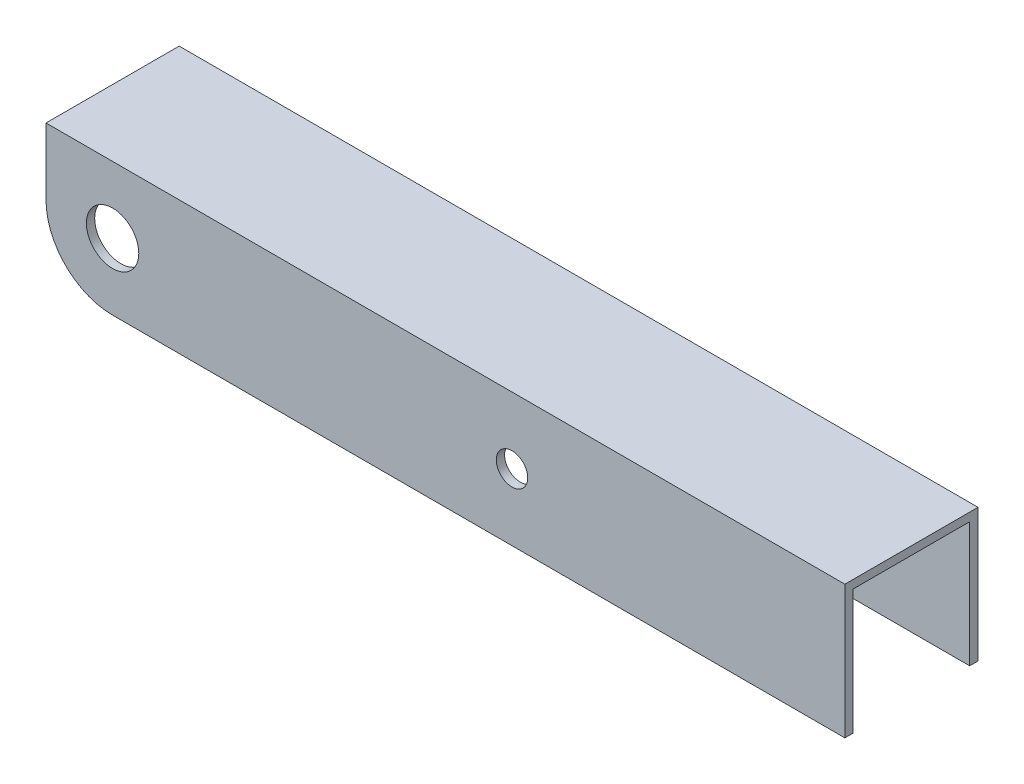
SolidWorks part; units mm, degrees
material "6061-T6 (SS)"
ref_plane "Front Plane" through (0, 0, 0) normal (0, 0, 1) x (1, 0, 0)
ref_plane "Top Plane" through (0, 0, 0) normal (0, 1, 0) x (1, 0, 0)
ref_plane "Right Plane" through (0, 0, 0) normal (1, 0, 0) x (0, 0, -1)
sketch "Sketch1" plane through (0, 0, 0) normal (1, 0, 0) x (0, 0, -1)
  line L1 (0, 0) -> (25.4, 0)
  line L2 (0, 0) -> (0, 50.8)
  line L3 (0, 50.8) -> (25.4, 50.8)
  line L4 (25.4, 0) -> (25.4, 50.8)
  line L5 (1.5875, 1.5875) -> (23.8125, 1.5875)
  line L6 (1.5875, 1.5875) -> (1.5875, 49.2125)
  line L7 (1.5875, 49.2125) -> (23.8125, 49.2125)
  line L8 (23.8125, 1.5875) -> (23.8125, 49.2125)
  dimension "D1" = 50.8
  dimension "D2" = 25.4
  dimension "D3" = 1.5875
  dimension "D4" = 1.5875
  dimension "D5" = 1.5875
  dimension "D6" = 1.5875
extrude "Boss-Extrude1" add sketch "Sketch1" along normal blind 152.4
sketch "Sketch2" plane through (0, 0, 0) normal (0, 0, 1) x (1, 0, 0)
  line L1 (0, 50.8) -> (0, 0) construction
  line L3 (152.4, 50.8) -> (0, 50.8) construction
  line L4 (12.7, 25.4) -> (152.4, 25.4)
  line L5 (152.4, 50.8) -> (152.4, 0) construction
  line L7 (0, 38.1) -> (0, 0)
  line L8 (0, 0) -> (152.4, 0)
  line L9 (152.4, 0) -> (152.4, 25.4)
  line L10 (12.7, 38.1) -> (88.9, 38.1) construction
  circle A0 centre (12.7, 38.1) radius 5
  arc A1 (0, 38.1) -> (12.7, 25.4) centre (12.7, 38.1) ccw
  circle A2 centre (88.9, 38.1) radius 3
  dimension "D1" = 12.7
  dimension "D3" = 76.2
  dimension "D2" = 12.7
extrude "Cut-Extrude1" cut sketch "Sketch2" against normal blind 152.4
